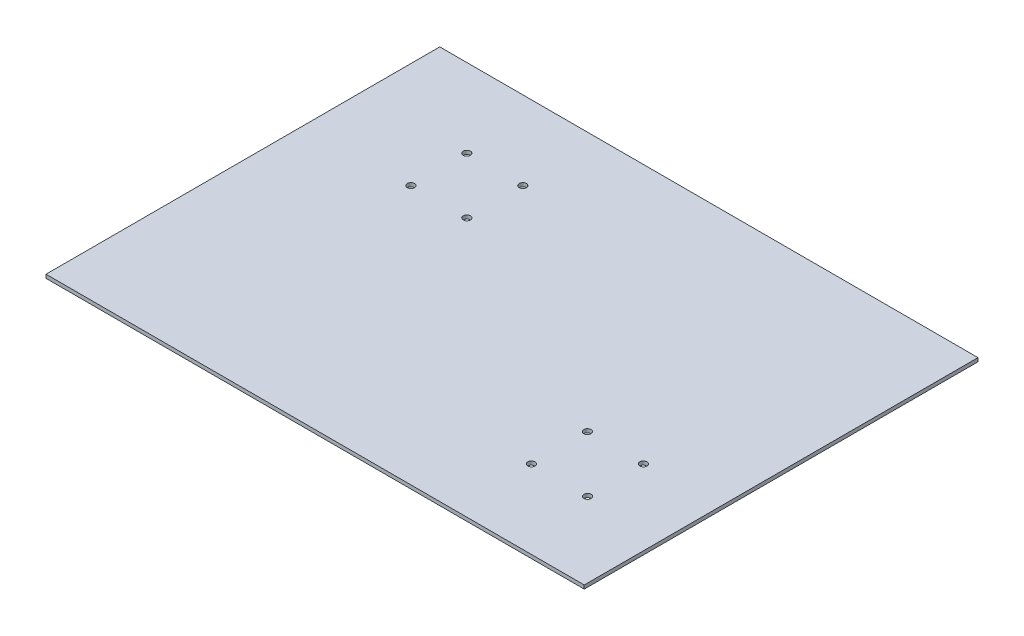
SolidWorks part; units mm, degrees
ref_plane "Front Plane" through (0, 0, 0) normal (0, 0, 1) x (1, 0, 0)
ref_plane "Top Plane" through (0, 0, 0) normal (0, 1, 0) x (1, 0, 0)
ref_plane "Right Plane" through (0, 0, 0) normal (1, 0, 0) x (0, 0, -1)
sketch "Sketch1" plane through (0, 0, 0) normal (1, 0, 0) x (0, 0, -1)
  line L0 (-26.6783, 0) -> (191.3217, 0)
  line L1 (119.9, 0) -> (-119.9, 0) construction
  line L2 (-26.6783, 0) -> (-26.6783, 2)
  line L3 (191.3217, 0) -> (191.3217, 2)
  line L4 (191.3217, 2) -> (-26.6783, 2)
  dimension "D1" = 218
  dimension "D2" = 2
extrude "Boss-Extrude1" add sketch "Sketch1" along normal blind 298 contours L4 L2 L0 L3
sketch "Sketch2" plane through (0, 2, 0) normal (0, 1, 0) x (1, 0, 0)
  circle A4 centre (89.5, 116.8217) radius 2
  circle A5 centre (58.5, 116.8217) radius 2
  circle A6 centre (89.5, 147.8217) radius 2
  circle A7 centre (58.5, 147.8217) radius 2
  circle A13 centre (256.3313, 47.7194) radius 2
  circle A14 centre (256.4575, 16.7194) radius 2
  circle A15 centre (225.3313, 16.7194) radius 2
  circle A16 centre (225.3313, 47.7194) radius 2
  dimension "D10" = 4
  dimension "D11" = 4
  dimension "D2" = 4
  dimension "D3" = 4
  dimension "D4" = 4
  dimension "D5" = 4
  dimension "D6" = 4
  dimension "D7" = 4
  dimension "D8" = 31
  dimension "D12" = 31
extrude "Cut-Extrude1" cut sketch "Sketch2" against normal blind 10
